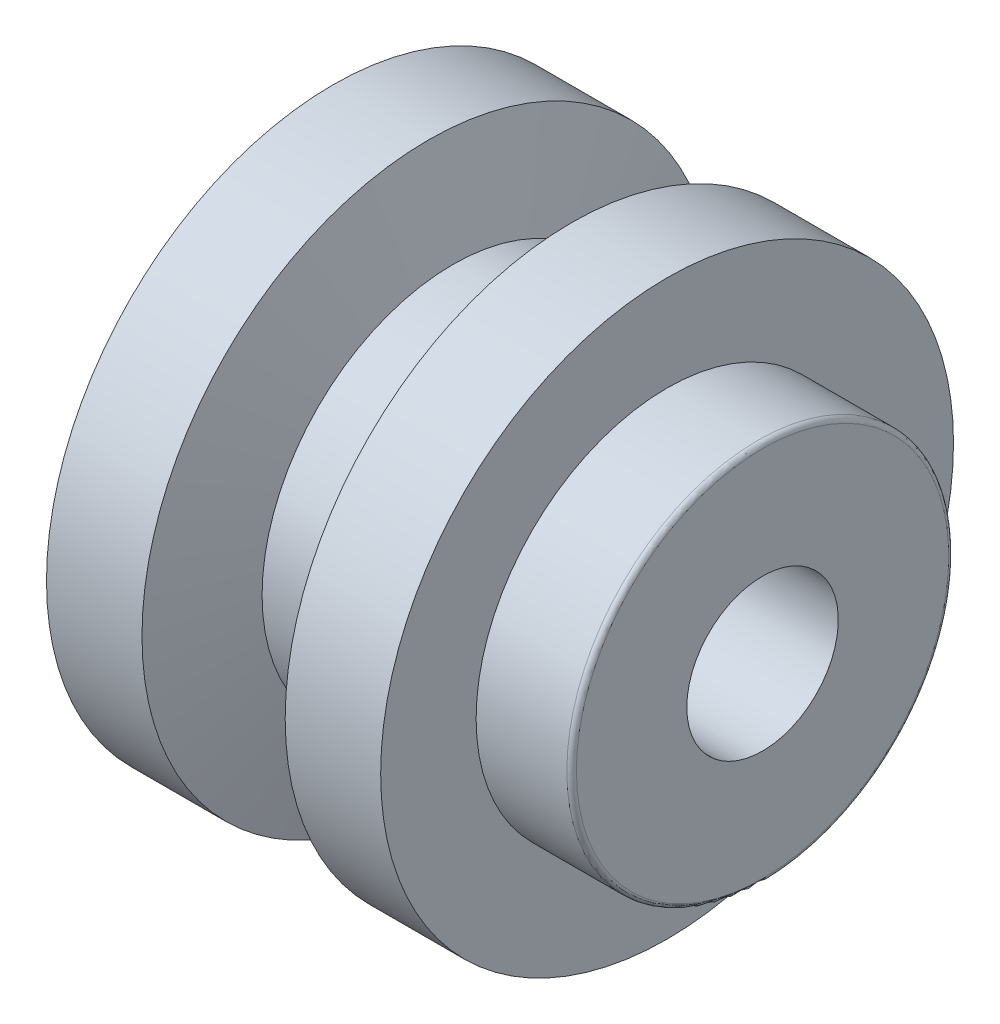
SolidWorks part; units mm, degrees
ref_plane "Front Plane" through (0, 0, 0) normal (0, 0, 1) x (1, 0, 0)
ref_plane "Top Plane" through (0, 0, 0) normal (0, 1, 0) x (1, 0, 0)
ref_plane "Right Plane" through (0, 0, 0) normal (1, 0, 0) x (0, 0, -1)
sketch "Sketch1" plane through (0, 0, 0) normal (0, 0, 1) x (1, 0, 0)
  line L0 (0, 0) -> (43.9763, 0) construction
  line L1 (0, -17.935) -> (0, -30)
  line L3 (10, -30) -> (12.5802, -20)
  line L4 (12.5802, -20) -> (22.3205, -20)
  line L5 (22.3205, -20) -> (25, -30)
  line L6 (25, -30) -> (35, -30)
  line L7 (35, -30) -> (35, -20)
  line L8 (35, -20) -> (44.5, -20)
  line L9 (45, -19.5) -> (45, -7.935)
  line L10 (45, -7.935) -> (2.5, -7.935)
  line L11 (0, -17.935) -> (2.5, -7.935)
  line L12 (10, -30) -> (0, -30)
  arc A0 (44.5, -20) -> (45, -19.5) centre (44.5, -19.5) ccw
  point P18 (35, -30)
  point P21 (25, -30)
  dimension "D11" = 0.5
  dimension "D1" = 15.87
  dimension "D2" = 40
  dimension "D3" = 75
  dimension "D4" = 60
  dimension "D5" = 75.532
  dimension "D6" = 15
  dimension "D7" = 10
  dimension "D8" = 10
  dimension "D9" = 40
  dimension "D10" = 45
  dimension "D12" = 2.5
  dimension "D13" = 10
revolve "Revolve1" add sketch "Sketch1" angle 360 about L0
